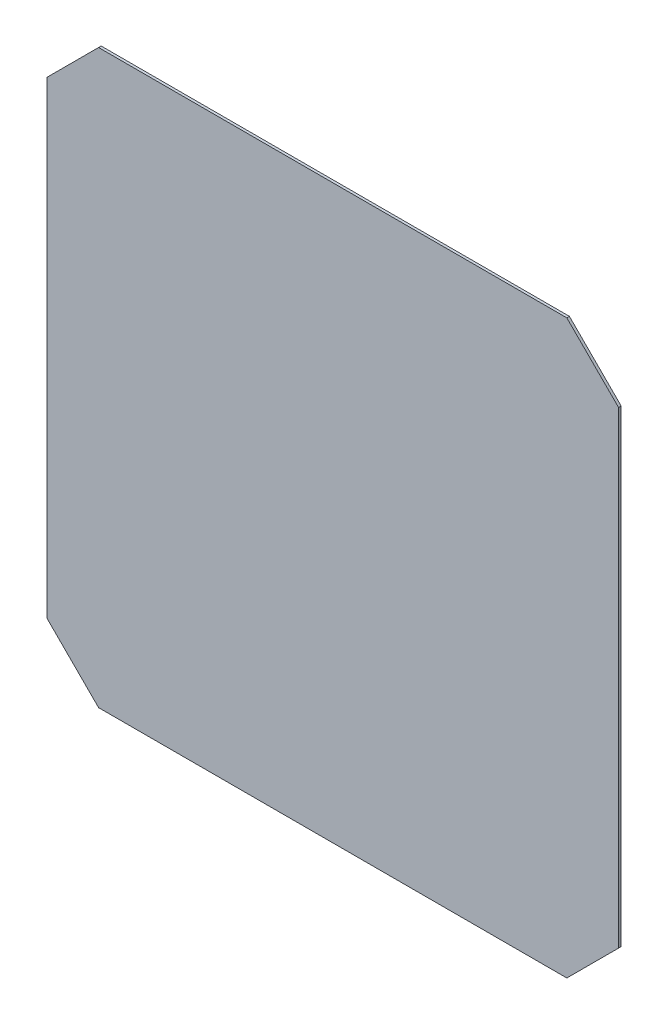
SolidWorks part; units mm, degrees
ref_plane "정면" through (0, 0, 0) normal (0, 0, 1) x (1, 0, 0)
ref_plane "윗면" through (0, 0, 0) normal (0, 1, 0) x (1, 0, 0)
ref_plane "우측면" through (0, 0, 0) normal (1, 0, 0) x (0, 0, -1)
sketch "스케치1" plane through (0, 0, 0) normal (0, 0, 1) x (1, 0, 0)
  line L0 (-221, 181) -> (-181, 221)
  line L1 (-181, 221) -> (181, 221)
  line L2 (-221, 181) -> (-221, -181)
  line L3 (-181, -221) -> (181, -221)
  line L4 (221, 181) -> (221, -181)
  line L5 (-221, 221) -> (221, -221) construction
  line L6 (-221, -221) -> (221, 221) construction
  line L7 (-221, -181) -> (-181, -221)
  line L8 (181, -221) -> (221, -181)
  line L9 (181, 221) -> (221, 181)
  point P4 (0, 0)
  dimension "D1" = 442
  dimension "D2" = 442
extrude "보스-돌출1" add sketch "스케치1" along normal blind 2
